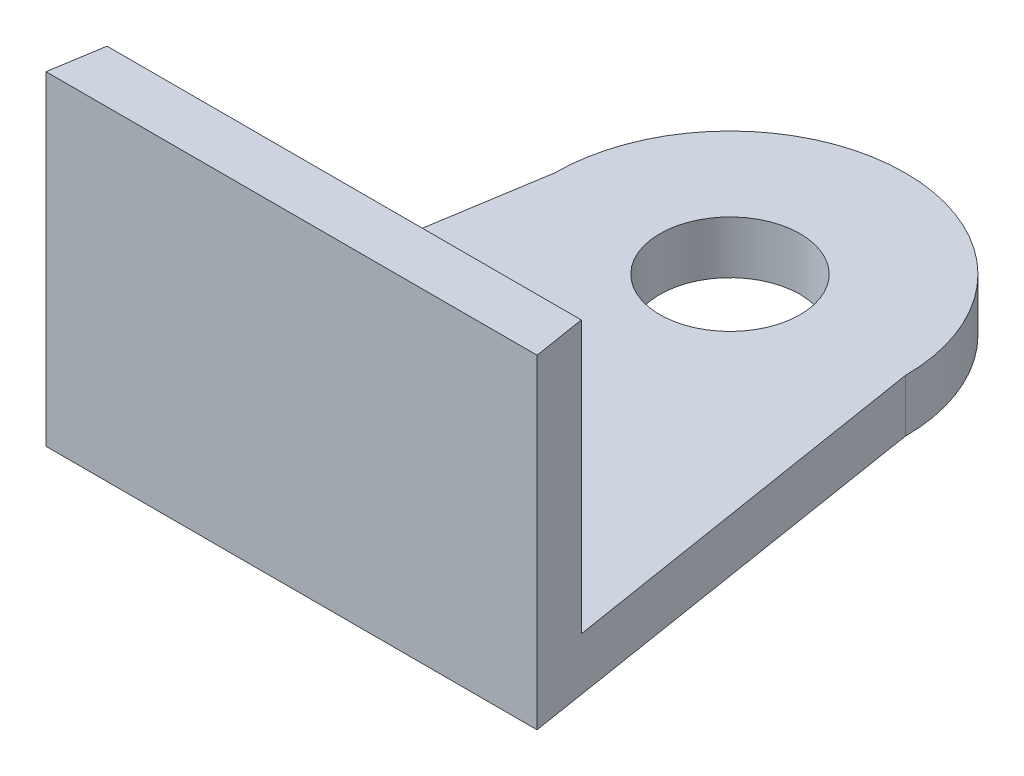
SolidWorks part; units mm, degrees
material "Custom Plastic"
ref_plane "Front Plane" through (0, 0, 0) normal (0, 0, 1) x (1, 0, 0)
ref_plane "Top Plane" through (0, 0, 0) normal (0, 1, 0) x (1, 0, 0)
ref_plane "Right Plane" through (0, 0, 0) normal (1, 0, 0) x (0, 0, -1)
sketch "Sketch1" plane through (0, 0, 0) normal (0, 1, 0) x (1, 0, 0)
  line L0 (-10, 0) -> (-14, -25)
  line L1 (10, 0) -> (14, -25)
  line L2 (0, 17.2103) -> (0, -39.4896) construction
  line L3 (-14, -25) -> (14, -25)
  arc A0 (-10, 0) -> (10, 0) centre (0, 0) cw
  dimension "D1" = 10
  dimension "D2" = 25
  dimension "D3" = 14
extrude "Boss-Extrude1" add sketch "Sketch1" along normal blind 3
sketch "Sketch2" plane through (0, 3, 0) normal (0, 1, 0) x (1, 0, 0)
  line L0 (-21.4034, 0) -> (30.5216, 0) construction
  circle A0 centre (0, 0) radius 4
  dimension "D1" = 8
extrude "Cut-Extrude1" cut sketch "Sketch2" against normal blind 13
sketch "Sketch5" plane through (0, 3, 0) normal (0, 1, 0) x (1, 0, 0)
  line L0 (-13.52, -22) -> (13.52, -22)
  line L1 (-10, 0) -> (-14, -25) construction
  line L2 (14, -25) -> (10, 0) construction
  line L3 (-13.52, -22) -> (-14, -25)
  line L4 (-14, -25) -> (14, -25)
  line L5 (14, -25) -> (13.52, -22)
  dimension "D1" = 3
extrude "Boss-Extrude2" add sketch "Sketch5" along normal blind 15.5
sketch "Sketch6" plane through (0, 3, 0) normal (0, 1, 0) x (1, 0, 0)
  circle A0 centre (0, 0) radius 4.6
  dimension "D1" = 9.2
extrude "Cut-Extrude4" cut sketch "Sketch6" against normal blind 1.5
sketch "Sketch7" plane through (0, 1.5, 0) normal (0, 1, 0) x (1, 0, 0)
  circle A0 centre (0, 0) radius 4 construction
  circle A1 centre (0, 0) radius 4.6
  circle A2 centre (0, 0) radius 4.6
  circle A3 centre (0, 0) radius 4
  dimension "D1" = 0
extrude "Boss-Extrude3" add sketch "Sketch7" along normal up to surface (1.5 mm away) up to face at (0, 3, 4.6)
